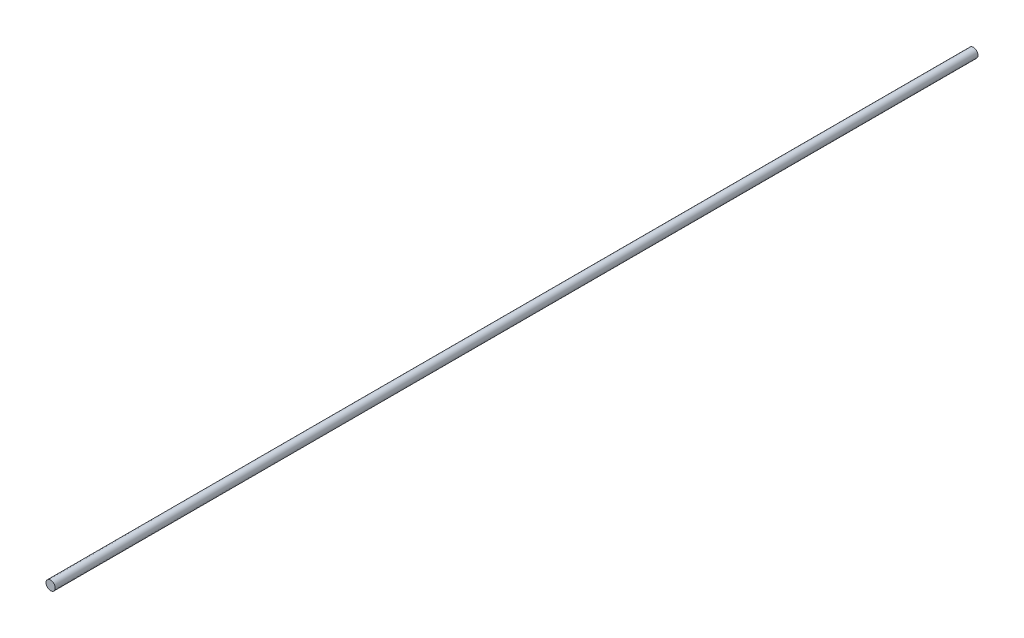
SolidWorks part; units mm, degrees
ref_plane "Front Plane" through (0, 0, 0) normal (0, 0, 1) x (1, 0, 0)
ref_plane "Top Plane" through (0, 0, 0) normal (0, 1, 0) x (1, 0, 0)
ref_plane "Right Plane" through (0, 0, 0) normal (1, 0, 0) x (0, 0, -1)
sketch "Sketch1" plane through (0, 0, 0) normal (0, 0, 1) x (1, 0, 0)
  circle A0 centre (0, 0) radius 1
  dimension "D1" = 2
extrude "Boss-Extrude1" add sketch "Sketch1" along normal blind 200
